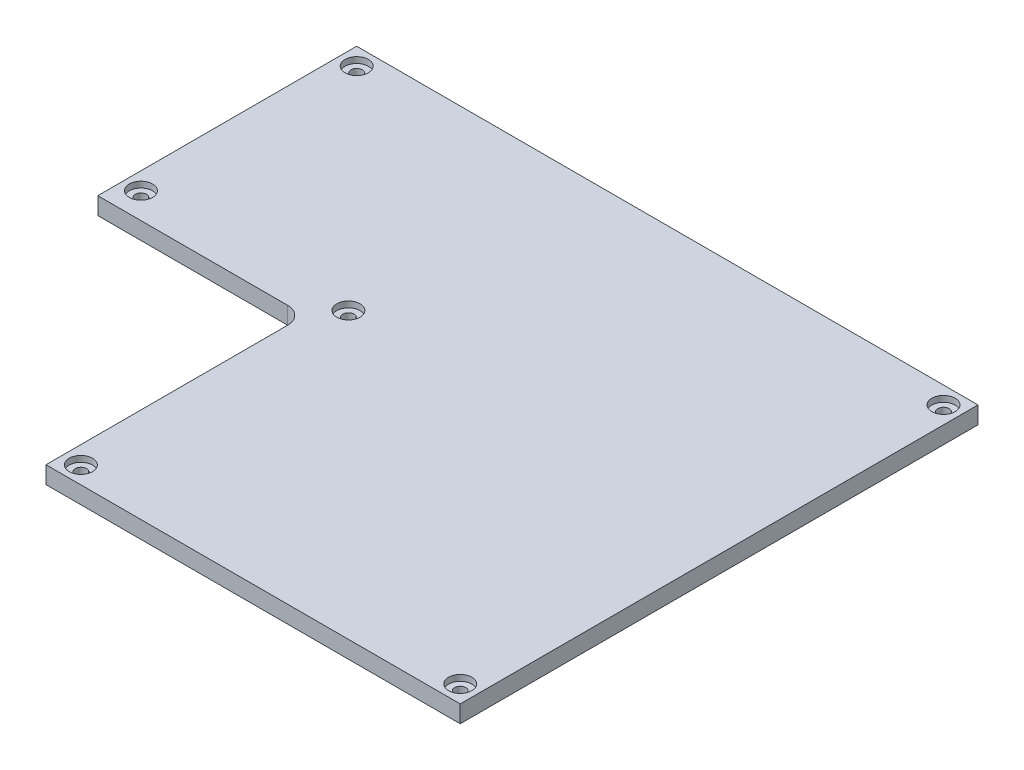
SolidWorks part; units mm, degrees
material "6063-T5"
ref_plane "Front Plane" through (0, 0, 0) normal (0, 0, 1) x (1, 0, 0)
ref_plane "Top Plane" through (0, 0, 0) normal (0, 1, 0) x (1, 0, 0)
ref_plane "Right Plane" through (0, 0, 0) normal (1, 0, 0) x (0, 0, -1)
sketch "Sketch1" plane through (0, 0, 0) normal (0, 1, 0) x (1, 0, 0)
  line L1 (-70.9559, 56.0294) -> (109.0441, 56.0294)
  line L2 (-70.9559, 56.0294) -> (-70.9559, -18.9706)
  line L3 (-70.9559, -18.9706) -> (-15.9559, -18.9706)
  line L4 (109.0441, 56.0294) -> (109.0441, -18.9706)
  line L5 (109.0441, -18.9706) -> (-10.9559, -18.9706)
  line L6 (109.0441, -18.9706) -> (109.0441, -93.9706)
  line L7 (109.0441, -93.9706) -> (-10.9559, -93.9706)
  line L8 (-10.9559, -23.9706) -> (-10.9559, -93.9706)
  arc A0 (-10.9559, -23.9706) -> (-15.9559, -18.9706) centre (-15.9559, -23.9706) ccw
  dimension "D4" = 5
  dimension "D1" = 75
  dimension "D2" = 180
  dimension "D3" = 120
extrude "Boss-Extrude1" add sketch "Sketch1" along normal blind 5
sketch "Sketch2" plane through (0, 5, 0) normal (0, 1, 0) x (1, 0, 0)
  line L0 (-70.9559, 56.0294) -> (109.0441, 56.0294) construction
  line L1 (-65.9559, 51.0294) -> (104.0441, 51.0294)
  line L2 (-65.9559, 51.0294) -> (-65.9559, -11.4706)
  line L3 (-65.9559, -11.4706) -> (104.0441, -11.4706)
  line L4 (104.0441, 51.0294) -> (104.0441, -11.4706)
  line L5 (104.0441, -11.4706) -> (-5.8459, -11.4706)
  line L6 (104.0441, -11.4706) -> (104.0441, -88.9706)
  line L7 (104.0441, -88.9706) -> (-5.8459, -88.9706)
  line L8 (-5.8459, -11.4706) -> (-5.8459, -88.9706)
  line L9 (109.0441, 56.0294) -> (109.0441, -93.9706) construction
  line L10 (109.0441, -93.9706) -> (-10.9559, -93.9706) construction
  line L12 (-10.9559, -23.9706) -> (-10.9559, -93.9706) construction
  line L13 (-70.9559, 56.0294) -> (-70.9559, -18.9706) construction
  dimension "D1" = 5
  dimension "D2" = 5
  dimension "D3" = 5
  dimension "D4" = 62.5
  dimension "D5" = 5.11
  dimension "D6" = 5
  dimension "D7" = 170
hole_wizard "CBORE for #4 Binding Head Machine Screw1" positions "Sketch3" profile "Sketch4" counterbore size "#4" standard "ANSI Inch" end condition up to next
sketch "Sketch3" plane through (0, 5, 0) normal (0, 1, 0) x (1, 0, 0)
  point P0 (-65.9559, 51.0294)
  point P3 (-65.9559, -11.4706)
  point P6 (-5.8459, -11.4706)
  point P9 (-5.8459, -88.9706)
  point P12 (104.0441, -88.9706)
  point P15 (104.0441, 51.0294)
sketch "Sketch4" plane through (-65.9559, 5, -51.0294) normal (1, 0, 0) x (0, 0, 1)
  line L0 (0, 0) -> (0, 5)
  line L1 (0, 5) -> (1.6319, 5)
  line L3 (1.6319, 5) -> (1.632, 1.7272)
  line L4 (1.632, 1.7272) -> (3.3731, 1.7272)
  line L5 (3.3731, 1.7272) -> (3.3731, 0)
  line L7 (3.3731, 0) -> (0, 0)
  line L11 (0, -6.35) -> (0, 107.95) construction
  dimension "Thru Hole Dia." = 3.2639
  dimension "Thru Hole Depth" = 5
  dimension "C'Bore Dia." = 6.7462
  dimension "C'Bore Depth" = 1.7272
